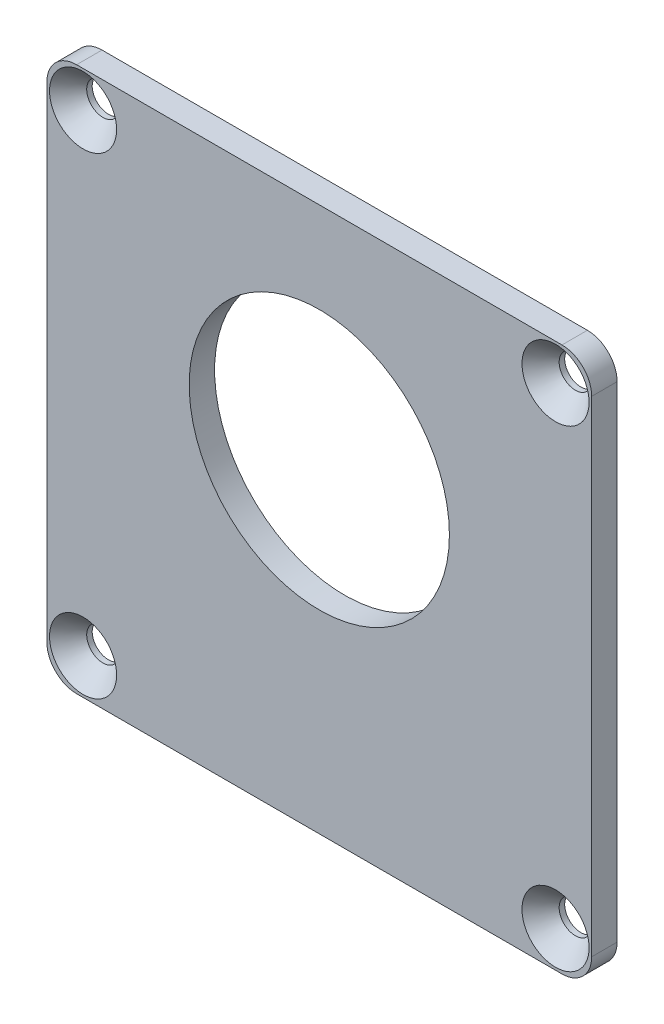
SolidWorks part; units mm, degrees
material "6061-T6 Al"
ref_plane "Front" through (0, 0, 0) normal (0, 0, 1) x (1, 0, 0)
ref_plane "Top" through (0, 0, 0) normal (0, 1, 0) x (1, 0, 0)
ref_plane "Right" through (0, 0, 0) normal (1, 0, 0) x (0, 0, -1)
sketch "Sketch1" plane through (0, 0, 0) normal (0, 0, 1) x (1, 0, 0)
  line L0 (-23.876, 26.797) -> (23.876, 26.797)
  line L1 (-26.797, 23.876) -> (-26.797, -23.876)
  line L2 (-23.876, -26.797) -> (23.876, -26.797)
  line L3 (26.797, 23.876) -> (26.797, -23.876)
  arc A0 (-26.797, -23.876) -> (-23.876, -26.797) centre (-23.876, -23.876) ccw
  arc A1 (23.876, -26.797) -> (26.797, -23.876) centre (23.876, -23.876) ccw
  arc A2 (23.876, 26.797) -> (26.797, 23.876) centre (23.876, 23.876) cw
  arc A3 (-26.797, 23.876) -> (-23.876, 26.797) centre (-23.876, 23.876) cw
  point P12 (0, 26.797)
  point P14 (-26.797, 0)
  dimension "D1" = 2.921
  dimension "D2" = 53.594
extrude "Boss-Extrude1" add sketch "Sketch1" along normal mid plane 2.5
hole_wizard "CSK for #4 Flat Head Machine Screw1" positions "Sketch6" profile "Sketch5" countersink size "#4" standard "ANSI Inch" end condition through all
sketch "Sketch6" plane through (0, 0, 1.25) normal (0, 0, 1) x (1, 0, 0)
  line L0 (-23.241, 23.241) -> (23.241, -23.241) construction
  line L1 (-23.241, 23.241) -> (23.241, 23.241) construction
  line L2 (23.241, 23.241) -> (23.241, -23.241) construction
  point P0 (-23.241, 23.241)
  point P1 (23.241, -23.241)
  point P6 (23.241, 23.241)
  point P10 (-23.241, -23.241)
  dimension "D1" = 46.482
sketch "Sketch5" plane through (-23.241, 23.241, 1.25) normal (1, 0, 0) x (0, -1, 0)
  line L0 (0, 0) -> (0, 2.5)
  line L1 (0, 2.5) -> (1.6002, 2.5)
  line L2 (1.6002, 2.5) -> (1.6002, 1.9577)
  line L3 (1.6002, 1.9577) -> (3.302, 0)
  line L5 (3.302, 0) -> (0, 0)
  line L6 (-1.6002, 1.9577) -> (-3.302, 0) construction
  line L11 (0, -6.35) -> (0, 107.95) construction
  dimension "Thru Hole Dia." = 3.2004
  dimension "Thru Hole Depth" = 2.5
  dimension "Near C'Sink Dia." = 6.604
  dimension "Near C'Sink Angle" = 82
sketch "Sketch7" plane through (0, 0, 1.25) normal (0, 0, 1) x (1, 0, 0)
  line L1 (-23.876, -26.797) -> (23.876, -26.797) construction
  circle A0 centre (0, 5.08) radius 12.8016
  dimension "D1" = 25.6032
  dimension "D2" = 31.877
extrude "Cut-Extrude1" cut sketch "Sketch7" against normal through all
